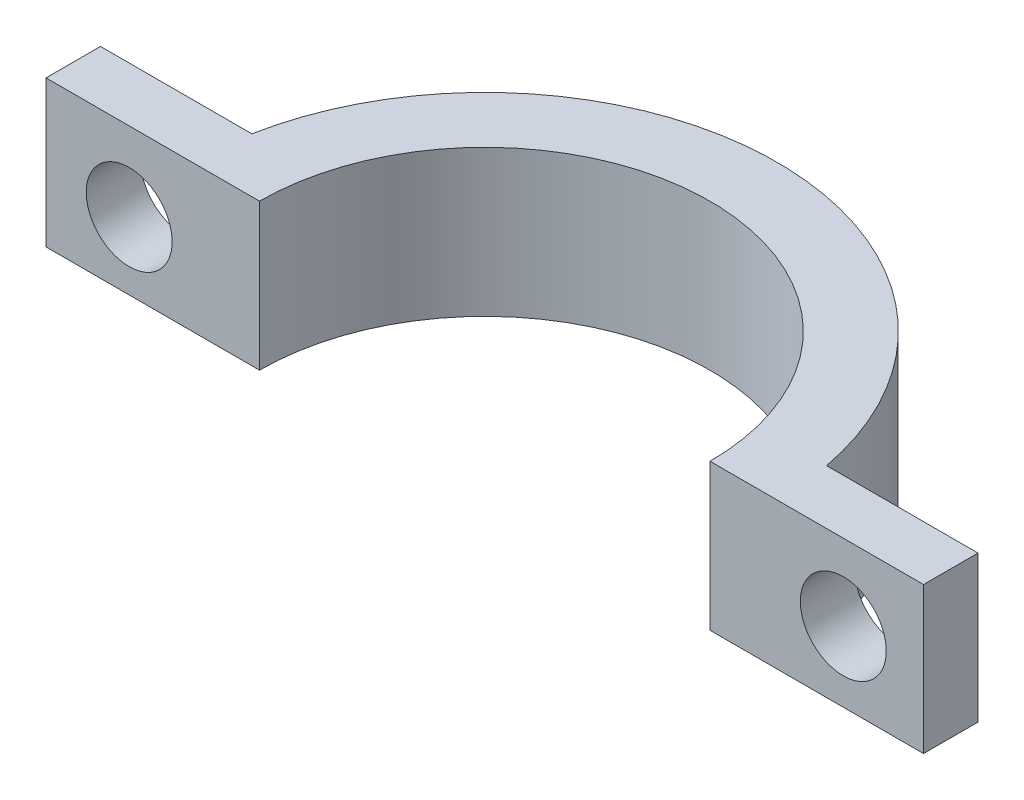
SolidWorks part; units mm, degrees
ref_plane "Спереди" through (0, 0, 0) normal (0, 0, 1) x (1, 0, 0)
ref_plane "Сверху" through (0, 0, 0) normal (0, 1, 0) x (1, 0, 0)
ref_plane "Справа" through (0, 0, 0) normal (1, 0, 0) x (0, 0, -1)
sketch "Эскиз1" plane through (0, 0, 0) normal (0, 1, 0) x (1, 0, 0)
  line L0 (-1000, 1.8455) -> (49000, 1.8455) construction
  line L1 (-38.9573, 1.8455) -> (38.9573, 1.8455)
  line L2 (-26, 6.6825) -> (-38.9573, 6.6825)
  line L3 (-38.9573, 6.6825) -> (-38.9573, 1.8455)
  line L5 (-26, 6.6825) -> (-25.5153, 6.6825)
  line L6 (0, -998.3143) -> (0, 49001.6857) construction
  line L8 (38.9573, 6.6825) -> (38.9573, 1.8455)
  line L9 (26, 6.6825) -> (38.9573, 6.6825)
  line L10 (26, 6.6825) -> (25.5153, 6.6825)
  arc A0 (20, 1.8455) -> (-20, 1.8455) centre (0, 1.8455) ccw
  arc A1 (25.5153, 6.6825) -> (-25.5153, 6.6825) centre (0, 1.8455) ccw
  point P7 (38.9573, 6.6825)
  point P9 (38.9573, 1.8455)
extrude "Бобышка-Вытянуть1" add sketch "Эскиз1" along normal blind 13 contours L10 A1 L5 L2 L3 L1 A0 L8 L9
sketch "Эскиз3" plane through (0, 0, -6.6825) normal (0, 0, -1) x (-1, 0, 0)
  line L0 (26.8113, 8.1162) -> (26.8113, 3.8117)
  line L1 (31.5714, 10.7978) -> (26.8113, 8.1162)
  line L2 (31.5714, 1.1346) -> (26.8113, 3.8162)
  line L3 (31.5714, 1.1346) -> (36.3315, 3.8162)
  line L4 (36.3315, 8.1162) -> (36.3315, 3.8117)
  line L5 (31.5714, 10.7978) -> (36.3315, 8.1162)
  line L6 (-36.5945, 8.3532) -> (-36.5945, 4.0487)
  line L7 (-31.8344, 11.0348) -> (-36.5945, 8.3532)
  line L8 (-31.8344, 1.3717) -> (-36.5945, 4.0532)
  line L9 (-31.8344, 1.3717) -> (-27.0743, 4.0532)
  line L10 (-27.0743, 8.3532) -> (-27.0743, 4.0487)
  line L11 (-31.8344, 11.0348) -> (-27.0743, 8.3532)
  circle A0 centre (31.5714, 5.9937) radius 3.8143
  circle A1 centre (-31.8344, 6.2308) radius 3.8143
extrude "Вырез-Вытянуть3" cut sketch "Эскиз3" against normal blind 13 contours A0 | A1
